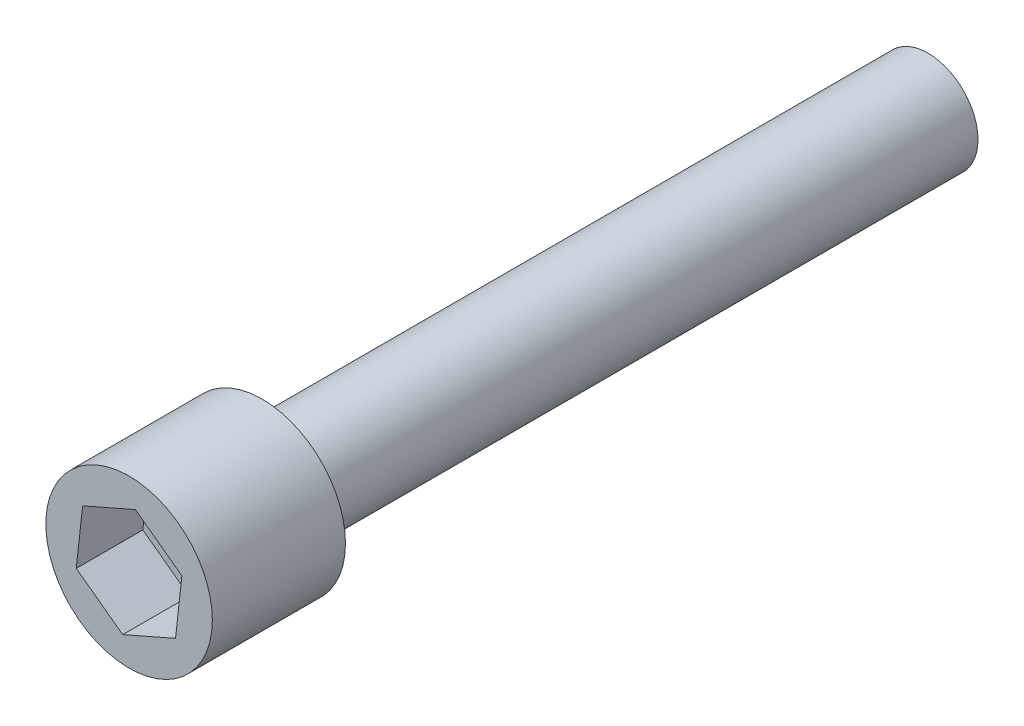
SolidWorks part; units mm, degrees
material "Stal nierdzewna (ferrytyczna)"
ref_plane "Płaszczyzna przednia" through (0, 0, 0) normal (0, 0, 1) x (1, 0, 0)
ref_plane "Płaszczyzna górna" through (0, 0, 0) normal (0, 1, 0) x (1, 0, 0)
ref_plane "Płaszczyzna prawa" through (0, 0, 0) normal (1, 0, 0) x (0, 0, -1)
sketch "Szkic1" plane through (0, 0, 0) normal (0, 0, 1) x (1, 0, 0)
  circle A0 centre (0, 0) radius 5
  dimension "D1" = 10
extrude "Dodanie-wyciągnięcie1" add sketch "Szkic1" along normal blind 8
sketch "Szkic2" plane through (0, 0, 0) normal (0, 0, 1) x (1, 0, 0)
  circle A0 centre (0, 0) radius 3
  dimension "D1" = 6
extrude "Dodanie-wyciągnięcie2" add sketch "Szkic2" against normal blind 40
sketch "Szkic3" plane through (0, 0, 8) normal (0, 0, 1) x (1, 0, 0)
  line L1 (2.7915, -2.0513) -> (3.1722, 1.3919)
  line L2 (3.1722, 1.3919) -> (0.3807, 3.4431)
  line L3 (0.3807, 3.4431) -> (-2.7915, 2.0513)
  line L4 (-2.7915, 2.0513) -> (-3.1722, -1.3919)
  line L5 (-3.1722, -1.3919) -> (-0.3807, -3.4431)
  line L6 (-0.3807, -3.4431) -> (2.7915, -2.0513)
  circle A0 centre (0, 0) radius 3 construction
  dimension "D1" = 6
extrude "Wytnij-wyciągnięcie1" cut sketch "Szkic3" against normal blind 4
